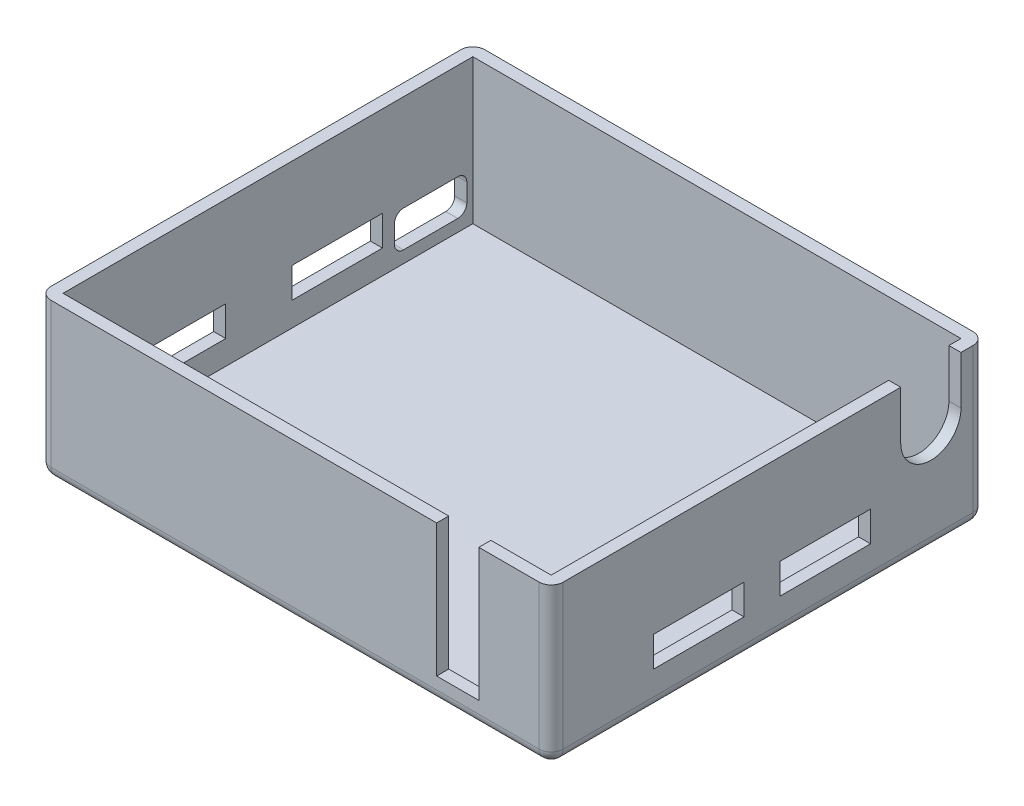
SolidWorks part; units mm, degrees
ref_plane "Plan de face" through (0, 0, 0) normal (0, 0, 1) x (1, 0, 0)
ref_plane "Plan de dessus" through (0, 0, 0) normal (0, 1, 0) x (1, 0, 0)
ref_plane "Plan de droite" through (0, 0, 0) normal (1, 0, 0) x (0, 0, -1)
sketch "Esquisse1" plane through (0, 0, 0) normal (0, 1, 0) x (1, 0, 0)
  line L0 (0, 36) -> (0, -36) construction
  line L5 (-42.5, 36) -> (42.5, 36)
  line L6 (-42.5, 36) -> (-42.5, -36)
  line L7 (-42.5, -36) -> (42.5, -36)
  line L8 (42.5, 36) -> (42.5, -36)
  dimension "D1" = 85
  dimension "D2" = 72
extrude "Boss.-Extru.1" add sketch "Esquisse1" along normal blind 26
shell "Coque1" thickness 2
sketch "Esquisse2" plane through (42.5, 0, 0) normal (1, 0, 0) x (0, 0, -1)
  line L0 (-36, 0) -> (36, 0) construction
  line L1 (36, 26) -> (36, 0) construction
  line L2 (-36, 26) -> (36, 26) construction
  line L3 (32, 26) -> (22, 26)
  line L4 (32, 26) -> (32, 18)
  line L5 (32, 18) -> (22, 18)
  line L6 (22, 26) -> (22, 18)
  circle A0 centre (27, 18) radius 5
  dimension "D1" = 10
  dimension "D2" = 18
  dimension "D3" = 9
extrude "Enlèv. mat.-Extru.1" cut sketch "Esquisse2" against normal blind 2 contours A0 | L4 L5 L6 L3
sketch "Esquisse3" plane through (42.5, 0, 0) normal (1, 0, 0) x (0, 0, -1)
  line L0 (-36, 0) -> (36, 0) construction
  line L1 (2, 11) -> (17, 11)
  line L2 (2, 11) -> (2, 6)
  line L3 (2, 6) -> (17, 6)
  line L4 (17, 11) -> (17, 6)
  line L5 (-19, 11) -> (-4, 11)
  line L6 (-19, 11) -> (-19, 6)
  line L7 (-19, 6) -> (-4, 6)
  line L8 (-4, 11) -> (-4, 6)
  line L9 (36, 26) -> (36, 0) construction
  dimension "D1" = 15
  dimension "D2" = 15
  dimension "D3" = 5
  dimension "D4" = 5
  dimension "D5" = 6
  dimension "D6" = 6
  dimension "D7" = 19
  dimension "D8" = 6
extrude "Enlèv. mat.-Extru.2" cut sketch "Esquisse3" against normal blind 2
sketch "Esquisse4" plane through (0, 0, 36) normal (0, 0, 1) x (1, 0, 0)
  line L0 (42.5, 26) -> (42.5, 0) construction
  line L1 (23.5, 26) -> (30.5, 26)
  line L2 (23.5, 26) -> (23.5, 4)
  line L3 (23.5, 4) -> (30.5, 4)
  line L4 (30.5, 26) -> (30.5, 4)
  line L5 (-42.5, 0) -> (42.5, 0) construction
  line L6 (-42.5, 26) -> (42.5, 26) construction
  dimension "D1" = 7
  dimension "D2" = 12
  dimension "D3" = 4
extrude "Enlèv. mat.-Extru.3" cut sketch "Esquisse4" against normal blind 2
sketch "Esquisse5" plane through (-42.5, 0, 0) normal (-1, 0, 0) x (0, 0, 1)
  line L0 (36, 26) -> (36, 0) construction
  line L1 (7, 11) -> (27, 11)
  line L2 (7, 11) -> (7, 6)
  line L3 (7, 6) -> (27, 6)
  line L4 (27, 11) -> (27, 6)
  line L5 (-36, 0) -> (36, 0) construction
  dimension "D1" = 20
  dimension "D2" = 9
  dimension "D3" = 5
  dimension "D4" = 6
extrude "Enlèv. mat.-Extru.4" cut sketch "Esquisse5" against normal blind 2
sketch "Esquisse6" plane through (-42.5, 0, 0) normal (-1, 0, 0) x (0, 0, 1)
  line L0 (-36, 0) -> (36, 0) construction
  line L1 (-19, 11) -> (-4, 11)
  line L2 (-19, 11) -> (-19, 6)
  line L3 (-19, 6) -> (-4, 6)
  line L4 (-4, 11) -> (-4, 6)
  line L5 (-36, 26) -> (-36, 0) construction
  dimension "D1" = 15
  dimension "D2" = 5
  dimension "D3" = 6
  dimension "D4" = 17
extrude "Enlèv. mat.-Extru.5" cut sketch "Esquisse6" against normal blind 2
sketch "Esquisse8" plane through (-42.5, 0, 0) normal (-1, 0, 0) x (0, 0, 1)
  line L0 (-36, 0) -> (36, 0) construction
  line L1 (-31.5, 10) -> (-22.5, 10)
  line L2 (-33, 8.5) -> (-33, 5.5)
  line L3 (-31.5, 4) -> (-22.5, 4)
  line L4 (-21, 8.5) -> (-21, 5.5)
  line L5 (-36, 26) -> (-36, 0) construction
  arc A0 (-22.5, 4) -> (-21, 5.5) centre (-22.5, 5.5) ccw
  arc A1 (-22.5, 10) -> (-21, 8.5) centre (-22.5, 8.5) cw
  arc A2 (-33, 5.5) -> (-31.5, 4) centre (-31.5, 5.5) ccw
  arc A3 (-31.5, 10) -> (-33, 8.5) centre (-31.5, 8.5) ccw
  point P6 (-21, 4)
  point P9 (-21, 10)
  point P14 (-33, 10)
  dimension "D3" = 1.5
  dimension "D1" = 12
  dimension "D2" = 6
  dimension "D4" = 4
  dimension "D5" = 3
extrude "Enlèv. mat.-Extru.7" cut sketch "Esquisse8" against normal blind 2
fillet "Congé1" radius 2 8 edges at (0, 0, 36) (42.5, 0, 0) (0, 0, -36) (-42.5, 0, 0) (-42.5, 13, -36) (42.5, 13, -36) (42.5, 13, 36) (-42.5, 13, 36)
